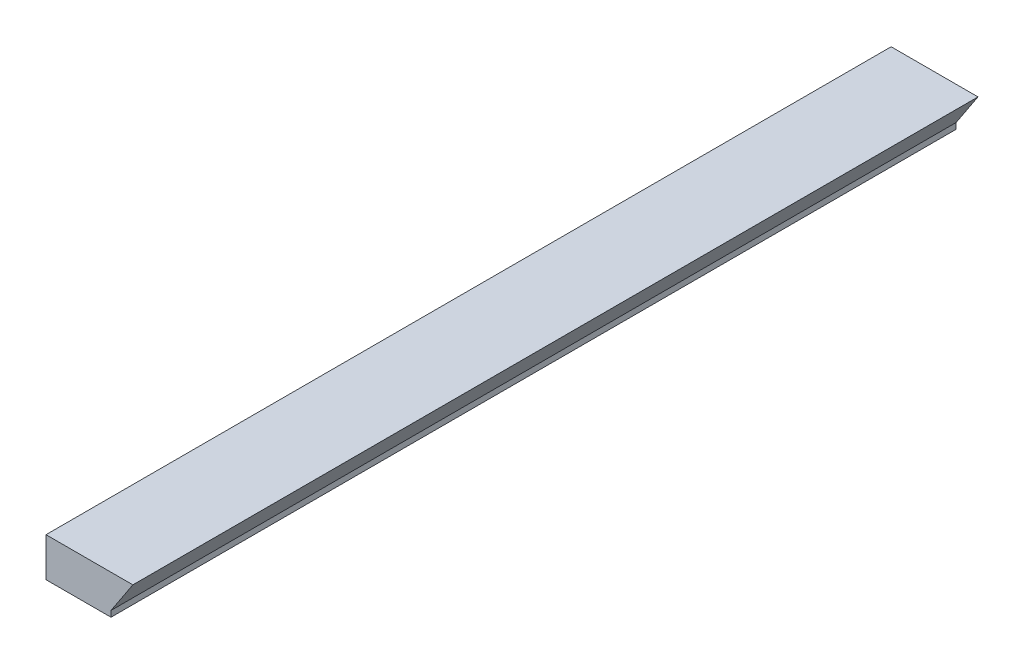
SolidWorks part; units mm, degrees
ref_plane "Front Plane" through (0, 0, 0) normal (0, 0, 1) x (1, 0, 0)
ref_plane "Top Plane" through (0, 0, 0) normal (0, 1, 0) x (1, 0, 0)
ref_plane "Right Plane" through (0, 0, 0) normal (1, 0, 0) x (0, 0, -1)
sketch "Sketch1" plane through (0, 0, 0) normal (0, 0, 1) x (1, 0, 0)
  line L0 (0, 0) -> (1.98, 3) construction
  line L1 (1.98, 3) -> (0, 3) construction
  line L2 (0, 3) -> (0, 0) construction
  line L3 (0, 3) -> (0, 0) construction
  line L4 (0, 3) -> (1.6805, 3)
  line L5 (1.6805, 3) -> (0, 0.4539)
  line L6 (0, 0.4539) -> (0, 0)
  line L7 (0, 0) -> (-5, 0)
  line L8 (-5, 0) -> (-5, 3)
  line L9 (-5, 3) -> (0, 3)
  dimension "D1" = 1.98
  dimension "D2" = 3
  dimension "D3" = 0.5
  dimension "D4" = 5
extrude "Boss-Extrude1" add sketch "Sketch1" along normal blind 65
